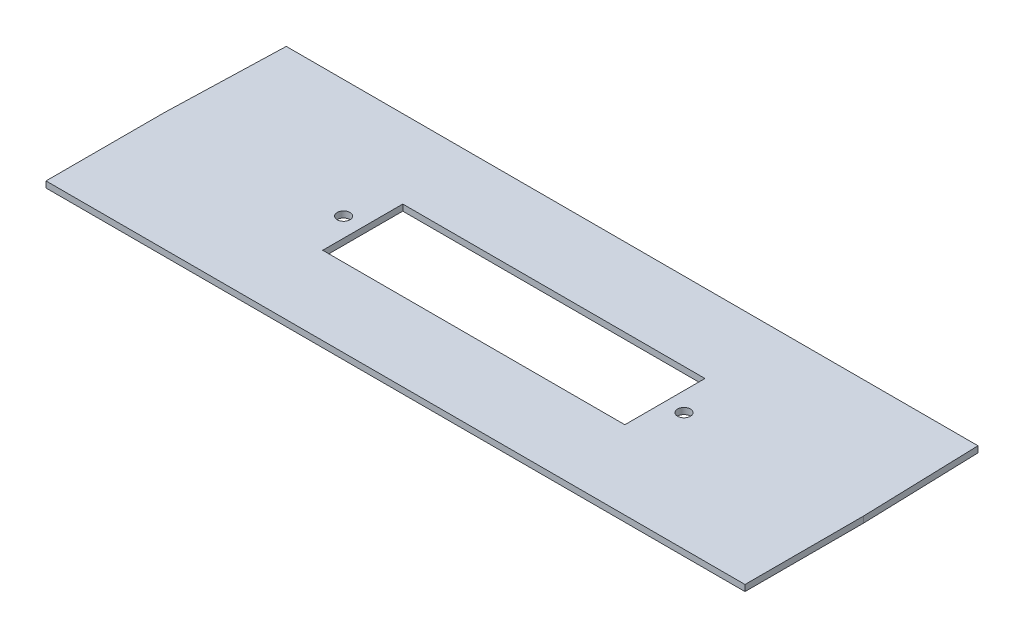
SolidWorks part; units mm, degrees
ref_plane "Front Plane" through (0, 0, 0) normal (0, 0, 1) x (1, 0, 0)
ref_plane "Top Plane" through (0, 0, 0) normal (0, 1, 0) x (1, 0, 0)
ref_plane "Right Plane" through (0, 0, 0) normal (1, 0, 0) x (0, 0, -1)
sketch "Sketch1" plane through (0, 0, 0) normal (0, 1, 0) x (1, 0, 0)
  line L0 (-96, 0) -> (-95, 32.5)
  line L1 (-95, 32.5) -> (95, 32.5)
  line L2 (-96, 0) -> (-96, -32.5)
  line L3 (-96, -32.5) -> (96, -32.5)
  line L4 (96, 0) -> (96, -32.5)
  line L5 (-96, 32.5) -> (96, -32.5) construction
  line L6 (-96, -32.5) -> (96, 32.5) construction
  line L7 (96, 0) -> (95, 32.5)
  point P0 (0, 0)
  dimension "D1" = 192
  dimension "D2" = 65
  dimension "D3" = 1
  dimension "D4" = 1
  dimension "D5" = 190
extrude "Boss-Extrude1" add sketch "Sketch1" along normal blind 1.7
sketch "Sketch2" plane through (0, 1.7, 0) normal (0, 1, 0) x (1, 0, 0)
  line L1 (-41.5, 11) -> (41.5, 11)
  line L2 (-41.5, 11) -> (-41.5, -11)
  line L3 (-41.5, -11) -> (41.5, -11)
  line L4 (41.5, 11) -> (41.5, -11)
  line L5 (-41.5, 11) -> (41.5, -11) construction
  line L6 (-41.5, -11) -> (41.5, 11) construction
  circle A0 centre (46.75, 0) radius 1.75
  circle A1 centre (-46.75, 0) radius 1.75
  point P0 (0, 0)
  dimension "D3" = 3.5
  dimension "D4" = 3.5
  dimension "D1" = 83
  dimension "D2" = 22
  dimension "D5" = 93.5
  dimension "D6" = 46.75
extrude "Cut-Extrude1" cut sketch "Sketch2" against normal blind 1.7
